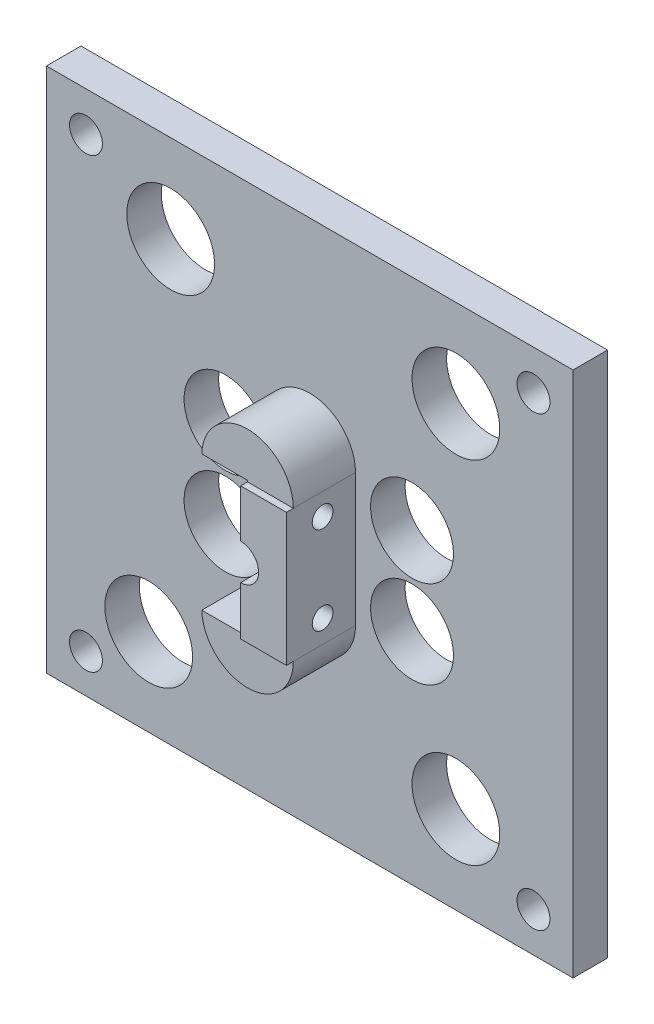
SolidWorks part; units mm, degrees
material "Hexcel AS4C (3000 Filaments)"
ref_plane "Front" through (0, 0, 0) normal (0, 0, 1) x (1, 0, 0)
ref_plane "Top" through (0, 0, 0) normal (0, 1, 0) x (1, 0, 0)
ref_plane "Right" through (0, 0, 0) normal (1, 0, 0) x (0, 0, -1)
sketch "Sketch4" plane through (0, 0, 0) normal (0, 0, 1) x (1, 0, 0)
  line L0 (0, -42.8625) -> (0, 41.275) construction
  line L1 (-49.15, -15.5) -> (-80.15, 15.5) construction
  line L2 (-80.15, -15.5) -> (-49.15, 15.5) construction
  line L3 (-39.925, 44.5615) -> (-39.925, -66.5635) construction
  line L4 (-71.275, 44.5615) -> (-71.275, -66.5635) construction
  line L8 (-62.05, 15.5) -> (-31.05, -15.5) construction
  line L9 (-31.05, 15.5) -> (-62.05, -15.5) construction
  line L11 (-31.05, 36.624) -> (-31.05, -53.8635) construction
  line L12 (43.75, 0) -> (-164.4633, 0) construction
  line L13 (-62.05, 36.624) -> (-62.05, -53.8635) construction
  line L14 (-49.15, 36.624) -> (-49.15, -53.8635) construction
  line L15 (-80.15, 36.624) -> (-80.15, -53.8635) construction
  line L16 (-113.2228, 15.5) -> (-0.2036, 15.5) construction
  line L17 (-113.2228, -15.5) -> (-0.2036, -15.5) construction
  line L18 (-25, -66.5635) -> (-25, 44.5615) construction
  line L19 (-68.1, -66.5635) -> (-68.1, 44.5615) construction
  line L20 (-43.1, 44.5615) -> (-43.1, -66.5635) construction
  line L21 (-86.2, -66.5635) -> (-86.2, 44.5615) construction
  line L22 (5.8397, -21.55) -> (-134.1626, -21.55) construction
  line L23 (5.8397, 21.55) -> (-134.1626, 21.55) construction
  line L24 (10.9249, -24.725) -> (-138.6228, -24.725) construction
  line L25 (10.9249, 24.725) -> (-138.6228, 24.725) construction
  line L26 (-89.375, 44.5615) -> (-89.375, -66.5635) construction
  line L27 (-21.825, 44.5615) -> (-21.825, -66.5635) construction
  circle A0 centre (0, 0) radius 12.7 construction
  circle A1 centre (0, 0) radius 15.875 construction
  circle A2 centre (0, 0) radius 9.46 construction
  circle A3 centre (-93.65, 0) radius 9.46 construction
  arc A4 (-93.65, 12.7) -> (-93.65, -12.7) centre (-93.65, 0) ccw construction
  circle A5 centre (27.27, 0) radius 9.46 construction
  circle A6 centre (27.27, 0) radius 12.7 construction
  circle A7 centre (-120.3675, 0) radius 9.46 construction
  circle A8 centre (-120.3675, 0) radius 12.7 construction
  point P3 (0, 0)
  point P6 (-49.15, -15.5)
  point P11 (-93.65, 0)
  point P12 (-49.15, 15.5)
  point P13 (-46.55, 0)
  point P14 (-80.15, 15.5)
  point P15 (-80.15, -15.5)
  point P61 (-64.65, 0)
  point P65 (27.27, 0)
  point P66 (-120.3675, 0)
  dimension "D20" = 3.175
  dimension "D18" = 29
  dimension "D26" = 73.82
  dimension "D27" = 64.65
  dimension "D2" = 31
  dimension "D3" = 25
  dimension "D4" = 31
  dimension "D5" = 21.825
  dimension "D6" = 15.5
  dimension "D7" = 15.5
  dimension "D8" = 6.05
  dimension "D9" = 6.05
  dimension "D10" = 6.05
  dimension "D11" = 6.05
  dimension "D12" = 6.05
  dimension "D13" = 6.05
  dimension "D14" = 3.175
  dimension "D15" = 3.175
  dimension "D16" = 3.175
  dimension "D17" = 3.175
  dimension "D19" = 3.175
  dimension "D21" = 3.175
  dimension "D22" = 46.55
  dimension "D23" = 47.1
  dimension "D24" = 58.32
  dimension "D25" = 147.6375
sketch "Sketch5" plane through (0, 0, 0) normal (0, 0, 1) x (1, 0, 0)
  line L0 (-46.55, 1.6) -> (-46.55, -2.6) construction
  line L4 (-46.55, -2.6) -> (-46.55, -9.6636)
  line L5 (-46.55, 9.525) -> (-39.925, 9.525)
  line L7 (-39.925, 44.5615) -> (-39.925, -66.5635) construction
  line L8 (-39.925, -9.6636) -> (-39.925, 9.525)
  line L9 (-46.55, -9.6636) -> (-39.925, -9.6636)
  line L13 (-46.55, 9.525) -> (-46.55, 2.6)
  circle A0 centre (-46.55, 0) radius 2.6 construction
  arc A1 (-46.55, 2.6) -> (-46.55, -2.6) centre (-46.55, 0) cw
extrude "Extrude1" add sketch "Sketch5" along normal blind 10
sketch "Sketch7" plane through (-39.925, 0, 0) normal (1, 0, 0) x (0, 0, -1)
  line L0 (0, -9.6636) -> (0, 9.525) construction
  circle A0 centre (-4.7625, 6.35) radius 1.5
  circle A1 centre (-4.7625, -6.35) radius 1.5
  dimension "D1" = 4.7625
extrude "Extrude3" cut sketch "Sketch7" against normal up to surface (6.625 mm away) up to face at (-46.55, 6.0625, 5)
sketch "Sketch6" plane through (0, 0, 0) normal (0, 0, -1) x (-1, 0, 0)
  line L0 (14.17, 50.8) -> (14.17, -98.425) construction
  line L1 (78.93, 63.5) -> (78.93, -95.3388) construction
  line L2 (84.65, 61.9125) -> (84.65, -95.25) construction
  line L3 (8.45, 55.5625) -> (8.45, -109.5375) construction
  line L4 (125.4125, 32.38) -> (-41.8258, 32.38) construction
  line L5 (123.825, 38.1) -> (-50.9969, 38.1) construction
  line L6 (119.0625, -38.1) -> (-36.5125, -38.1) construction
  line L7 (119.0625, -32.38) -> (-42.8625, -32.38) construction
  line L9 (84.65, 38.1) -> (8.45, 38.1)
  line L10 (84.65, 38.1) -> (84.65, -37.9954)
  line L11 (84.65, -37.9954) -> (8.45, -38.1)
  line L12 (8.45, 38.1) -> (8.45, -38.1)
  circle A0 centre (78.93, -32.38) radius 2.3813
  circle A1 centre (14.17, -32.38) radius 2.3812
  circle A2 centre (14.17, 32.38) radius 2.3812
  circle A3 centre (78.93, 32.38) radius 2.3813
  circle A4 centre (46.55, 0) radius 2.6
  circle A5 centre (69.85, -25.4) radius 6.35
  circle A6 centre (66.675, 25.4) radius 6.35
  circle A7 centre (25.4, 25.4) radius 6.35
  circle A8 centre (25.4, -25.4) radius 6.35
  circle A9 centre (58.7375, -6.35) radius 6
  circle A10 centre (58.7375, 6.35) radius 6
  circle A11 centre (31.75, -6.35) radius 6
  circle A12 centre (31.75, 6.35) radius 6
  dimension "D1" = 38.1
  dimension "D2" = 5.72
  dimension "D3" = 38.1
  dimension "D4" = 5.72
  dimension "D5" = 38.1
  dimension "D6" = 38.1
  dimension "D7" = 5.72
  dimension "D8" = 5.72
extrude "Extrude2" add sketch "Sketch6" along normal blind 5
sketch "Sketch9" plane through (0, 0, 0) normal (0, 0, 1) x (1, 0, 0)
  line L0 (-53.175, -9.6636) -> (-39.925, -9.6636)
  line L1 (-39.925, 9.525) -> (-53.175, 9.525)
  arc A0 (-39.925, -9.6636) -> (-53.175, -9.6636) centre (-46.55, -9.6636) cw
  arc A1 (-39.925, 9.525) -> (-53.175, 9.525) centre (-46.55, 9.525) ccw
extrude "Extrude4" add sketch "Sketch9" along normal blind 9
sketch "Sketch10" plane through (0, 0, 9) normal (0, 0, 1) x (1, 0, 0)
  line L0 (-46.55, 9.525) -> (-46.55, 9.725)
  line L1 (-46.55, -9.6636) -> (-46.55, -9.8636)
  line L2 (-46.55, -9.8636) -> (-53.9976, -9.8636)
  line L3 (-53.9976, -9.8636) -> (-53.9976, 9.725)
  line L4 (-53.9976, 9.725) -> (-46.55, 9.725)
  line L5 (-46.55, -9.6636) -> (-46.55, 9.525)
extrude "Extrude5" cut sketch "Sketch10" against normal blind 9
